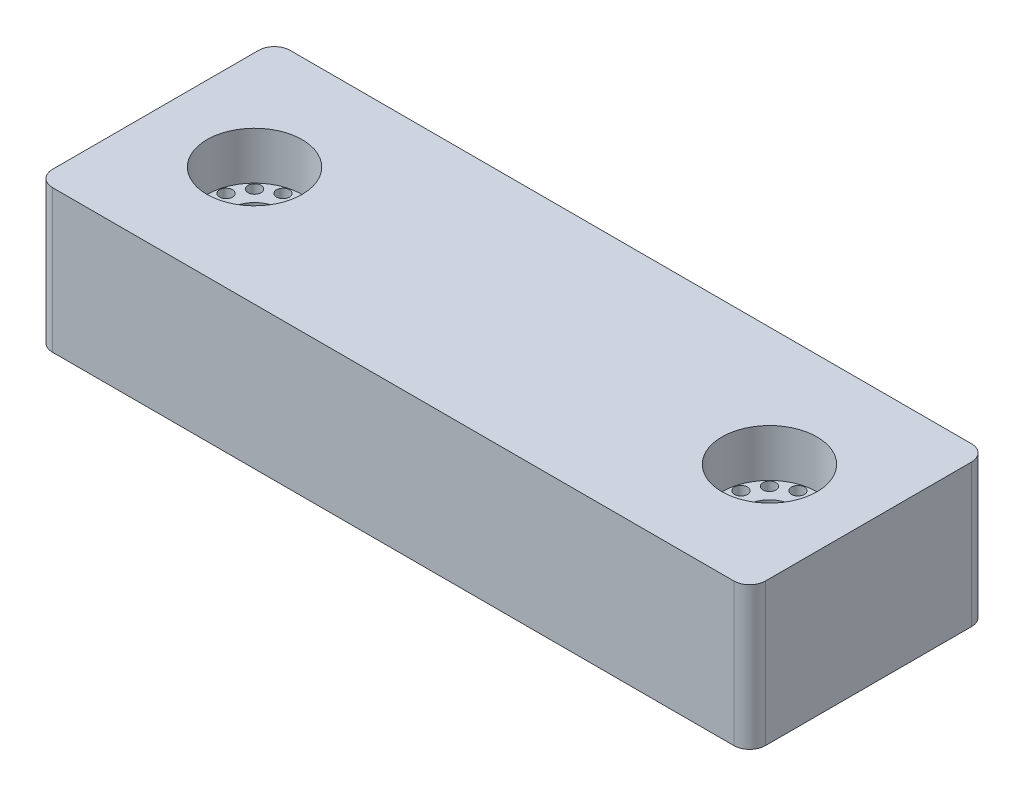
SolidWorks part; units mm, degrees
ref_plane "Front Plane" through (0, 0, 0) normal (0, 0, 1) x (1, 0, 0)
ref_plane "Top Plane" through (0, 0, 0) normal (0, 1, 0) x (1, 0, 0)
ref_plane "Right Plane" through (0, 0, 0) normal (1, 0, 0) x (0, 0, -1)
sketch "Sketch1" plane through (0, 0, 0) normal (0, 1, 0) x (1, 0, 0)
  line L0 (-45, 13) -> (-45, -13)
  line L3 (-43, -15) -> (43, -15)
  line L4 (45, -13) -> (45, 13)
  line L5 (43, 15) -> (-43, 15)
  line L6 (-32.5, 0) -> (32.5, 0) construction
  line L8 (-33.8159, 4.9109) -> (-36.095, 3.595) construction
  line L9 (-36.095, 3.595) -> (-37.4109, 1.3159) construction
  line L10 (-37.4109, 1.3159) -> (-37.4109, -1.3159) construction
  line L11 (-37.4109, -1.3159) -> (-36.095, -3.595) construction
  line L12 (-36.095, -3.595) -> (-33.8159, -4.9109) construction
  line L13 (-33.8159, -4.9109) -> (-31.1841, -4.9109) construction
  line L14 (-31.1841, -4.9109) -> (-28.905, -3.595) construction
  line L15 (-28.905, -3.595) -> (-27.5891, -1.3159) construction
  line L16 (-27.5891, -1.3159) -> (-27.5891, 1.3159) construction
  line L17 (-27.5891, 1.3159) -> (-28.905, 3.595) construction
  line L18 (-28.905, 3.595) -> (-31.1841, 4.9109) construction
  line L19 (-31.1841, 4.9109) -> (-33.8159, 4.9109) construction
  line L20 (33.8159, 4.9109) -> (31.1841, 4.9109) construction
  line L21 (31.1841, 4.9109) -> (28.905, 3.595) construction
  line L22 (28.905, 3.595) -> (27.5891, 1.3159) construction
  line L23 (27.5891, 1.3159) -> (27.5891, -1.3159) construction
  line L24 (27.5891, -1.3159) -> (28.905, -3.595) construction
  line L25 (28.905, -3.595) -> (31.1841, -4.9109) construction
  line L26 (31.1841, -4.9109) -> (33.8159, -4.9109) construction
  line L27 (33.8159, -4.9109) -> (36.095, -3.595) construction
  line L28 (36.095, -3.595) -> (37.4109, -1.3159) construction
  line L29 (37.4109, -1.3159) -> (37.4109, 1.3159) construction
  line L30 (37.4109, 1.3159) -> (36.095, 3.595) construction
  line L31 (36.095, 3.595) -> (33.8159, 4.9109) construction
  circle A2 centre (-32.5, 0) radius 3
  circle A3 centre (32.5, 0) radius 3
  circle A17 centre (32.5, 0) radius 6 construction
  circle A18 centre (-32.5, 0) radius 6 construction
  circle A19 centre (-31.1841, 4.9109) radius 0.9159 construction
  circle A20 centre (-31.1841, 4.9109) radius 0.8159
  circle A21 centre (-32.5, 0) radius 4.9109 construction
  circle A22 centre (-33.8159, 4.9109) radius 0.8159
  circle A23 centre (-33.8159, 4.9109) radius 1.8159 construction
  circle A24 centre (-36.095, 3.595) radius 0.8159
  circle A25 centre (-37.4109, 1.3159) radius 0.8159
  circle A26 centre (-37.4109, -1.3159) radius 0.8159
  circle A27 centre (-36.095, -3.595) radius 0.8159
  circle A28 centre (-33.8159, -4.9109) radius 0.8159
  circle A29 centre (-31.1841, -4.9109) radius 0.8159
  circle A30 centre (-28.905, -3.595) radius 0.8159
  circle A31 centre (-27.5891, -1.3159) radius 0.8159
  circle A32 centre (-27.5891, 1.3159) radius 0.8159
  circle A33 centre (-28.905, 3.595) radius 0.8159
  circle A34 centre (32.5, 0) radius 4.9109 construction
  circle A35 centre (31.1841, 4.9109) radius 0.8159
  circle A36 centre (33.8159, 4.9109) radius 0.8159
  circle A37 centre (36.095, 3.595) radius 0.8159
  circle A38 centre (37.4109, 1.3159) radius 0.8159
  circle A39 centre (37.4109, -1.3159) radius 0.8159
  circle A40 centre (36.095, -3.595) radius 0.8159
  circle A41 centre (33.8159, -4.9109) radius 0.8159
  circle A42 centre (31.1841, -4.9109) radius 0.8159
  circle A43 centre (28.905, -3.595) radius 0.8159
  circle A44 centre (27.5891, -1.3159) radius 0.8159
  circle A45 centre (27.5891, 1.3159) radius 0.8159
  circle A46 centre (28.905, 3.595) radius 0.8159
  arc A47 (43, -15) -> (45, -13) centre (43, -13) ccw
  arc A48 (-45, -13) -> (-43, -15) centre (-43, -13) ccw
  arc A49 (-45, 13) -> (-43, 15) centre (-43, 13) cw
  arc A50 (45, 13) -> (43, 15) centre (43, 13) ccw
  point P2 (-45, 0)
  point P6 (0, 15)
  point P72 (-45, 15)
  point P75 (45, 15)
  dimension "D1" = 90
  dimension "D2" = 12
  dimension "D3" = 65
  dimension "D4" = 6
  dimension "D5" = 30
  dimension "D6" = 0.1
  dimension "D7" = 1.6317
  dimension "D8" = 1
  dimension "D9" = 2
extrude "Boss-Extrude1" add sketch "Sketch1" along normal blind 18
sketch "Sketch2" plane through (0, 18, 0) normal (0, 1, 0) x (1, 0, 0)
  circle A0 centre (32.5, 0) radius 6 construction
  circle A1 centre (-32.5, 0) radius 6 construction
  circle A2 centre (32.5, 0) radius 6
  circle A3 centre (-32.5, 0) radius 6
extrude "Cut-Extrude1" cut sketch "Sketch2" against normal blind 6
